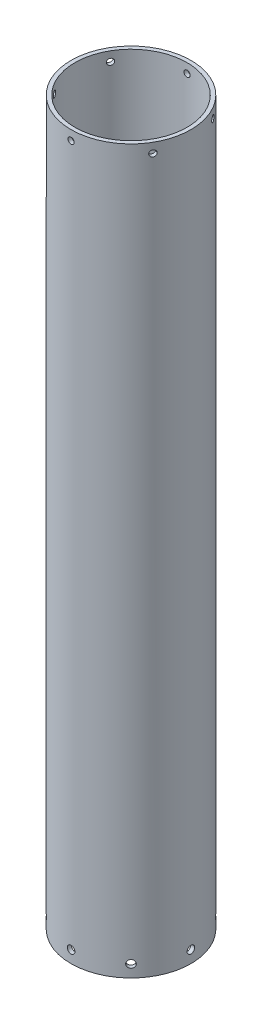
SolidWorks part; units mm, degrees
ref_plane "Front Plane" through (0, 0, 0) normal (0, 0, 1) x (1, 0, 0)
ref_plane "Top Plane" through (0, 0, 0) normal (0, 1, 0) x (1, 0, 0)
ref_plane "Right Plane" through (0, 0, 0) normal (1, 0, 0) x (0, 0, -1)
sketch "Sketch2" plane through (0, 0, 0) normal (0, 1, 0) x (1, 0, 0)
  circle A0 centre (0, 0) radius 18
  circle A1 centre (0, 0) radius 19.25
  dimension "D1" = 1.25
extrude "Boss-Extrude1" add sketch "Sketch2" along normal blind 231.82
sketch "Sketch3" plane through (0, 0, 0) normal (0, 0, 1) x (1, 0, 0)
  circle A0 centre (0, 3.92) radius 1.205
  point P2 (0, 0)
  dimension "D1" = 3.92
extrude "Cut-Extrude2" cut sketch "Sketch3" against normal blind 231.82 contours A0
pattern_circular "CirPattern3" count 8 over 360 about axis through (0, 231.82, 0) along (0, -1, 0) of "Cut-Extrude2"
sketch "Sketch4" plane through (0, 0, 0) normal (0, 0, 1) x (1, 0, 0)
  line L1 (19.25, 231.82) -> (-19.25, 231.82) construction
  circle A1 centre (0, 228.73) radius 0.992
  point P0 (0, 228.074)
  dimension "D1" = 3.09
extrude "Cut-Extrude3" cut sketch "Sketch4" along normal blind 231.82
pattern_circular "CirPattern4" count 6 over 360 about axis through (0, 231.82, 0) along (0, -1, 0) of "Cut-Extrude3"
